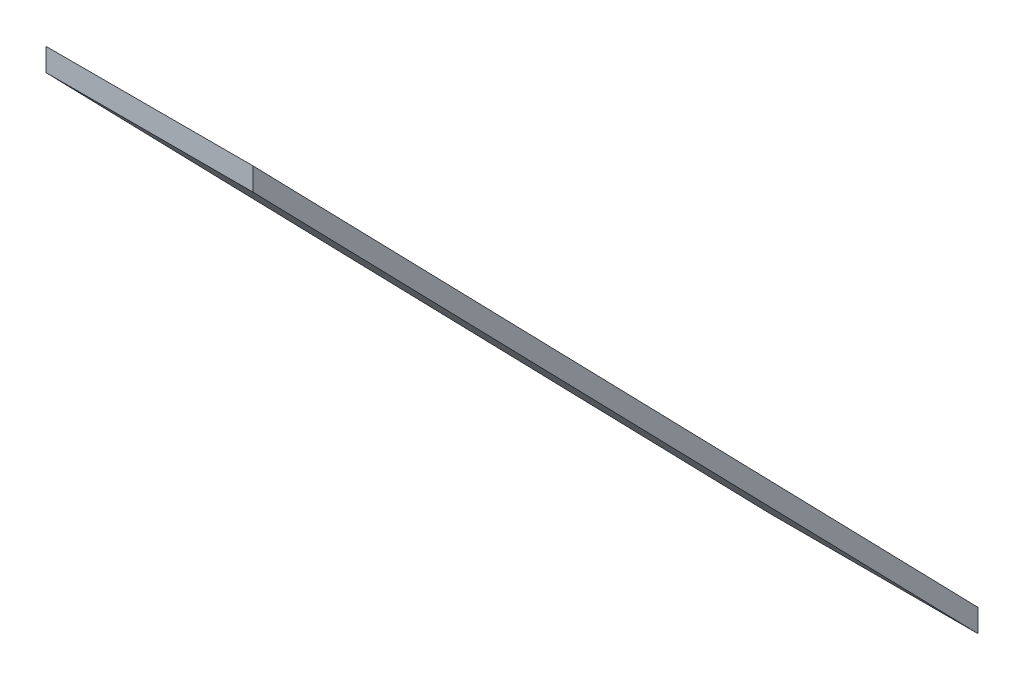
SolidWorks part; units mm, degrees
ref_plane "Front Plane" through (0, 0, 0) normal (0, 0, 1) x (1, 0, 0)
ref_plane "Top Plane" through (0, 0, 0) normal (0, 1, 0) x (1, 0, 0)
ref_plane "Right Plane" through (0, 0, 0) normal (1, 0, 0) x (0, 0, -1)
sketch "Sketch6" plane through (0, 0, 0) normal (0, 0, 1) x (1, 0, 0)
  line L1 (500, -55) -> (-500, -55)
  line L2 (500, -55) -> (500, 55)
  line L3 (500, 55) -> (-500, 55)
  line L4 (-500, -55) -> (-500, 55)
  line L5 (500, -55) -> (-500, 55) construction
  line L6 (500, 55) -> (-500, -55) construction
  point P0 (0, 0)
  dimension "D1" = 1000
  dimension "D2" = 110
sketch "Sketch7" plane through (0, 0, 0) normal (1, 0, 0) x (0, 0, -1)
  line L1 (0, -55) -> (0, 55) construction
  line L2 (0, 55) -> (0, -55) construction
  line L4 (-3500, 3541) -> (0, -55)
ref_plane "Plane2" through (0, 0, 3500) normal (0, 0, 1) x (1, 0, 0)
sketch "Sketch9" plane through (0, 0, 3500) normal (0, 0, 1) x (1, 0, 0)
  line L4 (-500, 3651) -> (500, 3651)
  line L5 (-500, 3651) -> (-500, 3541)
  line L6 (-500, 3541) -> (500, 3541)
  line L7 (500, 3651) -> (500, 3541)
  line L8 (-500, 3651) -> (500, 3541) construction
  line L9 (-500, 3541) -> (500, 3651) construction
  dimension "D1" = 1000
  dimension "D2" = 110
sweep "Sweep3" add profiles "Sketch9" path "Sketch7"
